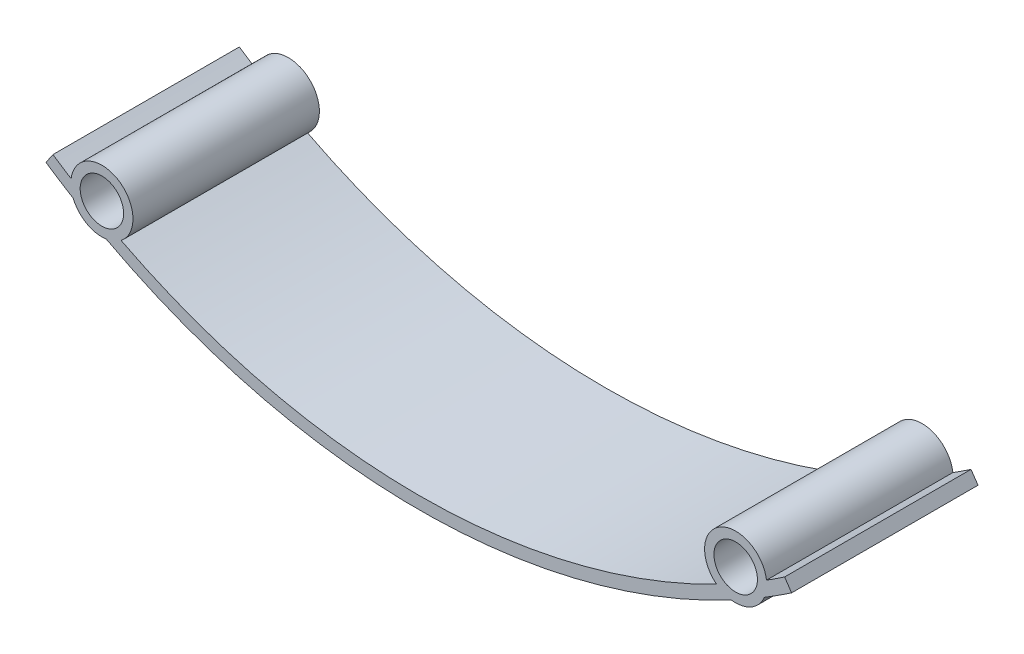
SolidWorks part; units mm, degrees
ref_plane "Front Plane" through (0, 0, 0) normal (0, 0, 1) x (1, 0, 0)
ref_plane "Top Plane" through (0, 0, 0) normal (0, 1, 0) x (1, 0, 0)
ref_plane "Right Plane" through (0, 0, 0) normal (1, 0, 0) x (0, 0, -1)
sketch "Sketch1" plane through (0, 0, 0) normal (0, 0, 1) x (1, 0, 0)
  line L0 (0, 107) -> (0, 0) construction
  line L1 (-60, 18.4054) -> (-58.8785, 20.0614)
  line L2 (0, 107) -> (-58.8785, 20.0614) construction
  line L5 (58.8785, 20.0614) -> (60, 18.4054)
  line L6 (58.8785, 20.0614) -> (0, 107) construction
  line L7 (-58.8785, 20.0614) -> (58.8785, 20.0614) construction
  line L8 (-51, 17.5126) -> (51, 17.5126) construction
  arc A0 (55.6152, 15.5891) -> (-55.6152, 15.5891) centre (0, 107) ccw construction
  arc A2 (58.8785, 20.0614) -> (55.9587, 18.1539) centre (0, 107) cw
  circle A3 centre (-51, 17.5126) radius 3.5
  circle A5 centre (51, 17.5126) radius 3.5
  arc A7 (60, 18.4054) -> (55.6152, 15.5891) centre (0, 107) cw
  arc A10 (-60, 18.4054) -> (-55.6152, 15.5891) centre (0, 107) ccw construction
  circle A11 centre (0, 107) radius 103 construction
  arc A12 (-47.9209, 13.5731) -> (-55.9587, 18.1539) centre (-51, 17.5126) ccw
  arc A13 (55.9587, 18.1539) -> (47.9209, 13.5731) centre (51, 17.5126) ccw
  arc A14 (-50.3027, 12.5614) -> (-47.9422, 11.3415) centre (0, 107) ccw construction
  arc A15 (-55.6152, 15.5891) -> (-60, 18.4054) centre (0, 107) cw
  arc A16 (-50.3027, 12.5614) -> (50.3027, 12.5614) centre (0, 107) ccw construction
  arc A17 (-55.9587, 18.1539) -> (-58.8785, 20.0614) centre (0, 107) cw
  arc A18 (-55.6152, 15.5891) -> (-50.3027, 12.5614) centre (-51, 17.5126) ccw
  arc A19 (50.3027, 12.5614) -> (-50.3027, 12.5614) centre (0, 107) cw
  arc A20 (55.6152, 15.5891) -> (60, 18.4054) centre (0, 107) ccw construction
  arc A21 (47.9209, 13.5731) -> (-47.9209, 13.5731) centre (0, 107) cw
  arc A22 (50.3027, 12.5614) -> (55.6152, 15.5891) centre (51, 17.5126) ccw
  point P14 (0, 17.5126)
  dimension "D1" = 214
  dimension "D3" = 105
  dimension "D4" = 102
  dimension "D6" = 7
  dimension "D7" = 10
  dimension "D5" = 206
  dimension "D2" = 120
extrude "Boss-Extrude1" add sketch "Sketch1" along normal blind 30
